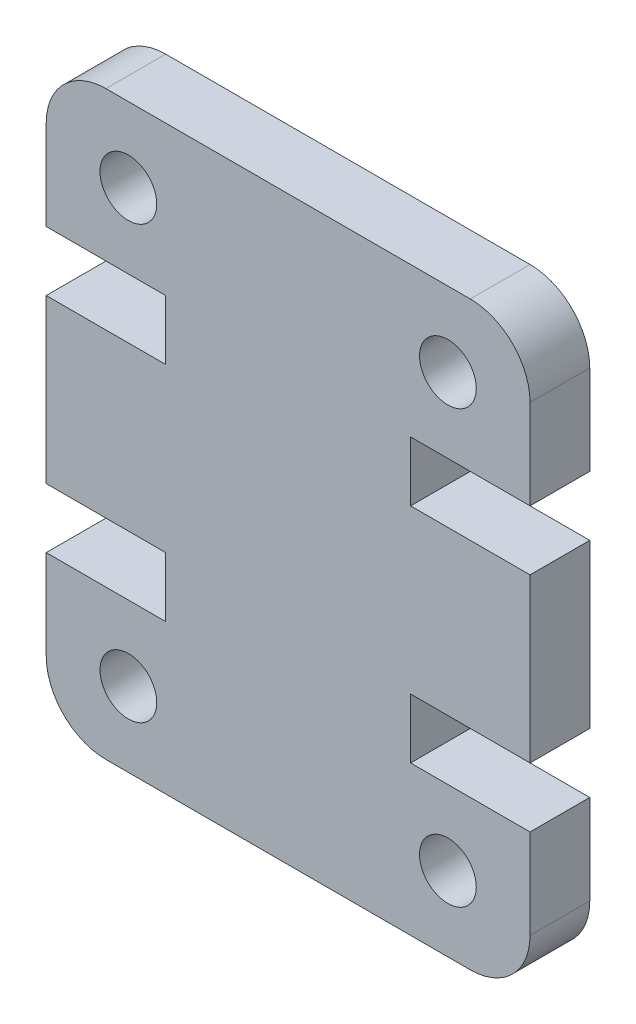
SolidWorks part; units mm, degrees
ref_plane "Front Plane" through (0, 0, 0) normal (0, 0, 1) x (1, 0, 0)
ref_plane "Top Plane" through (0, 0, 0) normal (0, 1, 0) x (1, 0, 0)
ref_plane "Right Plane" through (0, 0, 0) normal (1, 0, 0) x (0, 0, -1)
sketch "Sketch2" plane through (0, 0, 0) normal (0, 0, 1) x (1, 0, 0)
  line L0 (0, 7) -> (0, 12.455)
  line L1 (2, 0) -> (14.2, 0)
  line L2 (16.2, 5) -> (16.2, 2)
  line L3 (0, 9.7275) -> (16.2, 9.7275) construction
  line L4 (12.2, 5) -> (16.2, 5)
  line L5 (16.2, 7) -> (12.2, 7)
  line L6 (12.2, 7) -> (12.2, 5)
  line L7 (16.2, 7) -> (16.2, 12.455)
  line L8 (4, 7) -> (4, 5)
  line L9 (0, 14.455) -> (0, 17.455)
  line L10 (0, 7) -> (4, 7)
  line L11 (4, 5) -> (0, 5)
  line L12 (4, 14.455) -> (0, 14.455)
  line L13 (0, 12.455) -> (4, 12.455)
  line L14 (4, 12.455) -> (4, 14.455)
  line L15 (12.2, 12.455) -> (12.2, 14.455)
  line L16 (16.2, 12.455) -> (12.2, 12.455)
  line L17 (12.2, 14.455) -> (16.2, 14.455)
  line L18 (16.2, 14.455) -> (16.2, 17.455)
  line L19 (0, 5) -> (0, 2)
  line L20 (8.1, 19.455) -> (8.1, 0) construction
  line L21 (2, 19.455) -> (14.2, 19.455)
  circle A0 centre (13.45, 2.5) radius 0.95
  arc A1 (16.2, 2) -> (14.2, 0) centre (14.2, 2) cw
  circle A2 centre (2.75, 16.955) radius 0.95
  arc A3 (0, 2) -> (2, 0) centre (2, 2) ccw
  arc A4 (0, 17.455) -> (2, 19.455) centre (2, 17.455) cw
  circle A5 centre (2.75, 2.5) radius 0.95
  arc A6 (16.2, 17.455) -> (14.2, 19.455) centre (14.2, 17.455) ccw
  circle A7 centre (13.45, 16.955) radius 0.95
  point P18 (8.1, 9.7275)
  dimension "D1" = 1.9
  dimension "D2" = 2
  dimension "D3" = 2.75
  dimension "D4" = 8.1
  dimension "D5" = 2.5
  dimension "D6" = 5
  dimension "D8" = 9.7275
extrude "Boss-Extrude1" add sketch "Sketch2" along normal blind 4
sketch "Sketch3" plane through (0, 0, 4) normal (0, 0, 1) x (1, 0, 0)
  line L0 (0, 0) -> (16.2, 0)
  line L1 (16.2, 0) -> (16.2, 19.455)
  line L2 (16.2, 19.455) -> (0, 19.455)
  line L3 (0, 19.455) -> (0, 0)
extrude "Cut-Extrude1" cut sketch "Sketch3" against normal blind 2
equation "\"D4@Sketch2\"= \"fingerWidth@parametersSketch@prostheticParameters.SLDPRT\" / 2'Finger Width"
equation "\"D8@Sketch2\"= ( ( \"HL@parametersSketch@prostheticParameters.SLDPRT\" * 0.143 ) - 3 - 4 ) / 2 'MIP Length -SiliconeDIP-SiliconeMIP"
equation "\"D1@Sketch2\"= 1.5 + \"tol1@parametersSketch@prostheticParameters.SLDPRT\""
